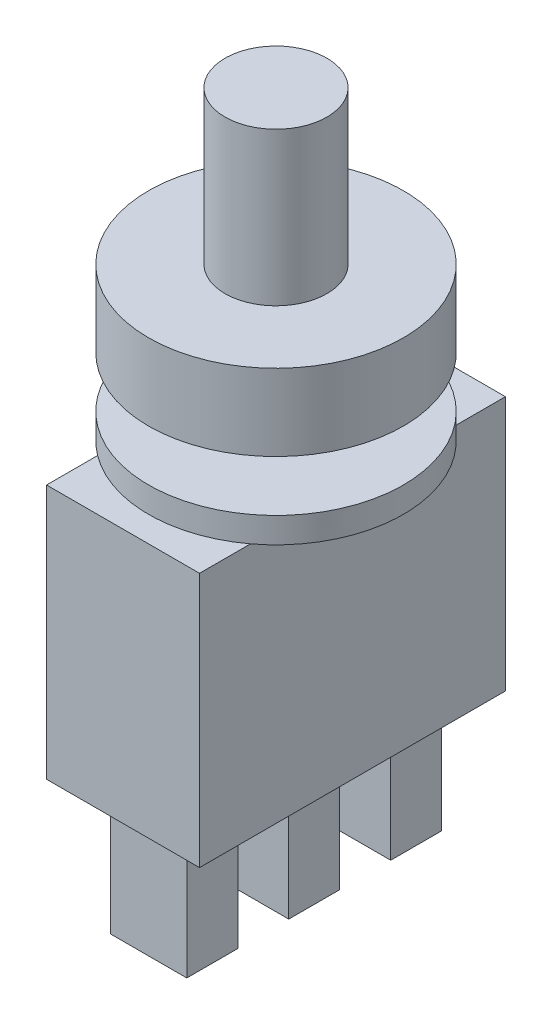
SolidWorks part; units mm, degrees
ref_plane "Plan de face" through (0, 0, 0) normal (0, 0, 1) x (1, 0, 0)
ref_plane "Plan de dessus" through (0, 0, 0) normal (0, 1, 0) x (1, 0, 0)
ref_plane "Plan de droite" through (0, 0, 0) normal (1, 0, 0) x (0, 0, -1)
sketch "Esquisse1" plane through (0, 0, 0) normal (0, 1, 0) x (1, 0, 0)
  circle A0 centre (0, 0) radius 5
  dimension "D1" = 10
extrude "Extrusion1" add sketch "Esquisse1" along normal blind 3
sketch "Esquisse2" plane through (0, 3, 0) normal (0, 1, 0) x (-1, 0, 0)
  circle A0 centre (0, 0) radius 2
  dimension "D1" = 4
extrude "Extrusion2" add sketch "Esquisse2" along normal blind 6
sketch "Esquisse3" plane through (0, 0, 0) normal (0, -1, 0) x (1, 0, 0)
  circle A0 centre (0, 0) radius 2
  dimension "D1" = 4
extrude "Extrusion3" add sketch "Esquisse3" along normal blind 2
sketch "Esquisse4" plane through (0, -2, 0) normal (0, -1, 0) x (1, 0, 0)
  circle A0 centre (0, 0) radius 5
  dimension "D1" = 10
extrude "Extrusion4" add sketch "Esquisse4" along normal blind 1
sketch "Esquisse5" plane through (0, -3, 0) normal (0, -1, 0) x (1, 0, 0)
  line L0 (0, 0) -> (0, 3.7815) construction
  line L1 (3, -6) -> (-3, -6)
  line L2 (3, -6) -> (3, 6)
  line L3 (3, 6) -> (-3, 6)
  line L4 (-3, -6) -> (-3, 6)
  line L5 (-1.6151, 0) -> (1.2087, 0) construction
  dimension "D1" = 6
  dimension "D2" = 3
  dimension "D3" = 6
  dimension "D4" = 12
extrude "Extrusion5" add sketch "Esquisse5" along normal blind 10
sketch "Esquisse6" plane through (0, -13, 0) normal (0, -1, 0) x (1, 0, 0)
  line L0 (0, 8.662) -> (0, -8.4735) construction
  line L1 (-1.5, 3) -> (1.5, 3)
  line L2 (-1.5, 3) -> (-1.5, 5)
  line L3 (-1.5, 5) -> (1.5, 5)
  line L4 (1.5, 3) -> (1.5, 5)
  line L5 (-1.5, -1) -> (1.5, -1)
  line L6 (-1.5, -1) -> (-1.5, 1)
  line L7 (-1.5, 1) -> (1.5, 1)
  line L8 (1.5, -1) -> (1.5, 1)
  line L9 (-1.5, -5) -> (1.5, -5)
  line L10 (-1.5, -5) -> (-1.5, -3)
  line L11 (-1.5, -3) -> (1.5, -3)
  line L12 (1.5, -5) -> (1.5, -3)
  line L13 (-5.4044, 0) -> (7.318, 0) construction
  dimension "D1" = 3
  dimension "D2" = 2
  dimension "D3" = 2
  dimension "D4" = 2
  dimension "D5" = 1
  dimension "D6" = 1.5
  dimension "D7" = 1.5
  dimension "D8" = 1.5
extrude "Extrusion6" add sketch "Esquisse6" along normal blind 5
